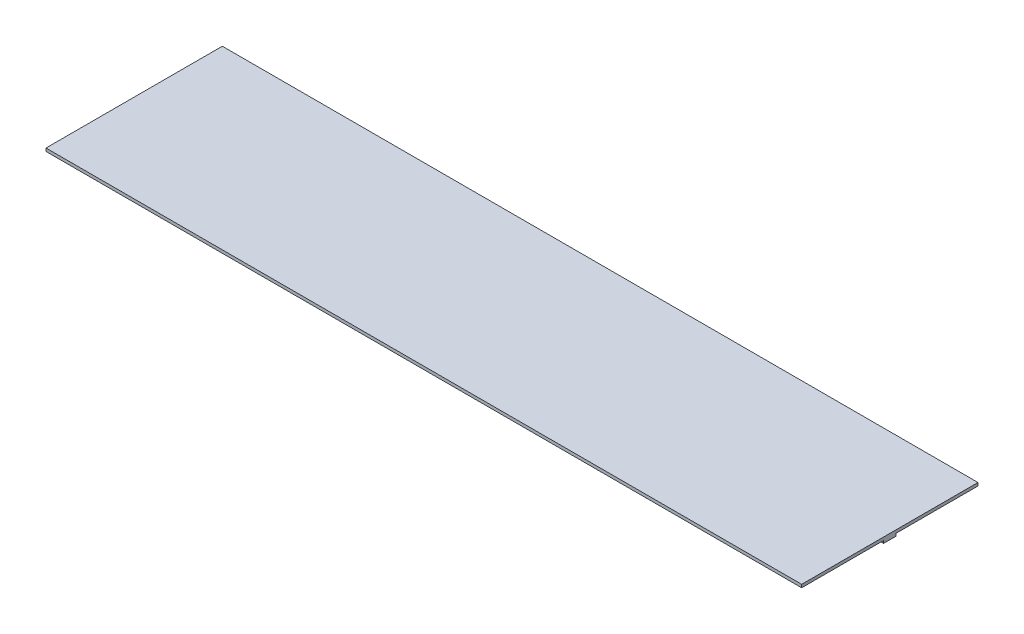
SolidWorks part; units mm, degrees
material "Nickel"
ref_plane "Front Plane" through (0, 0, 0) normal (0, 0, 1) x (1, 0, 0)
ref_plane "Top Plane" through (0, 0, 0) normal (0, 1, 0) x (1, 0, 0)
ref_plane "Right Plane" through (0, 0, 0) normal (1, 0, 0) x (0, 0, -1)
sketch "Sketch1" plane through (0, 0, 0) normal (0, 1, 0) x (1, 0, 0)
  line L1 (0, 0) -> (-30, 0)
  line L2 (0, 0) -> (0, -7)
  line L3 (0, -7) -> (-30, -7)
  line L4 (-30, 0) -> (-30, -7)
  dimension "D1" = 30
  dimension "D2" = 7
extrude "Boss-Extrude1" add sketch "Sketch1" along normal blind 0.12
sketch "Sketch2" plane through (0, 0, 0) normal (0, -1, 0) x (1, 0, 0)
  line L0 (0, 7) -> (0, 0) construction
  line L1 (0, 3.75) -> (-0.5, 3.75)
  line L2 (0, 3.75) -> (0, 3.25)
  line L3 (0, 3.25) -> (-0.5, 3.25)
  line L4 (-0.5, 3.75) -> (-0.5, 3.25)
  line L5 (0, 0) -> (-30, 0) construction
  point P6 (-0.5, 3.5)
  dimension "D1" = 3.5
  dimension "D2" = 0.5
  dimension "D3" = 0.5
extrude "Boss-Extrude2" add sketch "Sketch2" along normal blind 0.1
sketch "Sketch3" plane through (0, 0, 0) normal (0, -1, 0) x (1, 0, 0)
  line L0 (-30, 0) -> (-30, 7) construction
  line L1 (-30, 3.75) -> (-29.5, 3.75)
  line L2 (-30, 3.75) -> (-30, 3.25)
  line L3 (-30, 3.25) -> (-29.5, 3.25)
  line L4 (-29.5, 3.75) -> (-29.5, 3.25)
  line L5 (-30, 7) -> (0, 7) construction
  point P6 (-29.5, 3.5)
  dimension "D1" = 3.5
  dimension "D2" = 0.5
  dimension "D3" = 0.5
extrude "Boss-Extrude3" add sketch "Sketch3" along normal blind 0.1
